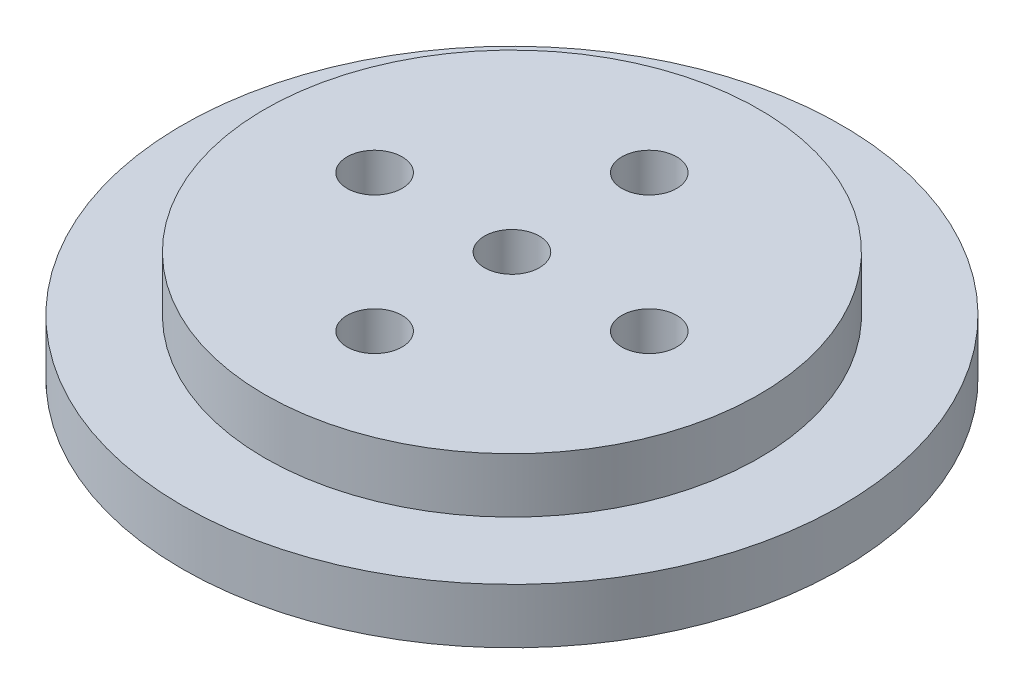
SolidWorks part; units mm, degrees
material "Plástico personalizado"
ref_plane "Alzado" through (0, 0, 0) normal (0, 0, 1) x (1, 0, 0)
ref_plane "Planta" through (0, 0, 0) normal (0, 1, 0) x (1, 0, 0)
ref_plane "Vista lateral" through (0, 0, 0) normal (1, 0, 0) x (0, 0, -1)
sketch "Croquis1" plane through (0, 0, 0) normal (0, 1, 0) x (1, 0, 0)
  line L0 (-45, 0) -> (0, 0) construction
  line L1 (0, 0) -> (45, 0) construction
  line L2 (0, 0) -> (0, 45) construction
  line L3 (0, 0) -> (0, -45) construction
  circle A0 centre (0, 0) radius 5
  circle A1 centre (0, 0) radius 45
  circle A2 centre (0, 25) radius 5
  circle A3 centre (25, 0) radius 5
  circle A4 centre (0, -25) radius 5
  circle A5 centre (-25, 0) radius 5
  dimension "D1" = 10
  dimension "D2" = 10
  dimension "D3" = 10
  dimension "D4" = 10
  dimension "D5" = 10
  dimension "D10" = 90
  dimension "D6" = 25
  dimension "D7" = 25
  dimension "D8" = 25
  dimension "D9" = 25
extrude "Saliente-Extruir1" add sketch "Croquis1" along normal blind 30
sketch "Croquis2" plane through (0, 30, 0) normal (0, 1, 0) x (1, 0, 0)
  circle A0 centre (0, 0) radius 60
  circle A1 centre (0, 0) radius 45
  dimension "D1" = 120
  dimension "D2" = 90
extrude "Saliente-Extruir2" add sketch "Croquis2" against normal blind 10 from offset 10
